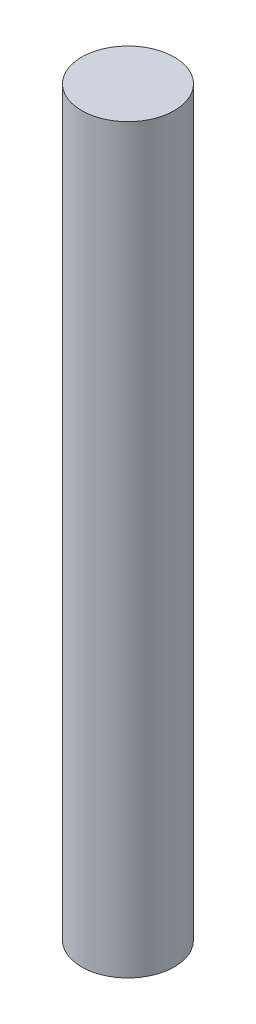
SolidWorks part; units mm, degrees
ref_plane "Front Plane" through (0, 0, 0) normal (0, 0, 1) x (1, 0, 0)
ref_plane "Top Plane" through (0, 0, 0) normal (0, 1, 0) x (1, 0, 0)
ref_plane "Right Plane" through (0, 0, 0) normal (1, 0, 0) x (0, 0, -1)
sketch "Sketch1" plane through (0, 0, 0) normal (0, 1, 0) x (1, 0, 0)
  circle A0 centre (0, 0) radius 6.35
  dimension "D1" = 12.7
extrude "Boss-Extrude1" add sketch "Sketch1" along normal blind 101.6
